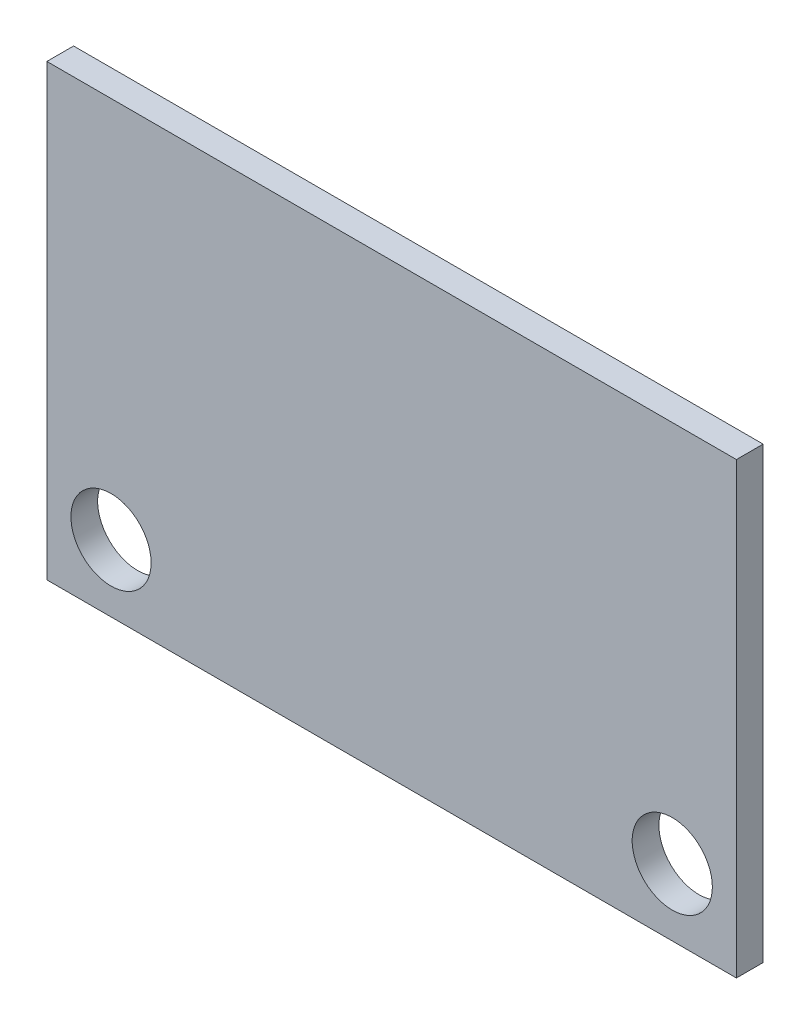
SolidWorks part; units mm, degrees
ref_plane "Alzado" through (0, 0, 0) normal (0, 0, 1) x (1, 0, 0)
ref_plane "Planta" through (0, 0, 0) normal (0, 1, 0) x (1, 0, 0)
ref_plane "Vista lateral" through (0, 0, 0) normal (1, 0, 0) x (0, 0, -1)
sketch "Croquis1" plane through (0, 0, 0) normal (0, 0, 1) x (1, 0, 0)
  line L0 (-10.5, -5.9) -> (10.5, -5.9) construction
  line L1 (12.9, -8.4) -> (-12.9, -8.4)
  line L2 (12.9, -8.4) -> (12.9, 8.4)
  line L3 (12.9, 8.4) -> (-12.9, 8.4)
  line L4 (-12.9, -8.4) -> (-12.9, 8.4)
  line L5 (12.9, -8.4) -> (-12.9, 8.4) construction
  line L6 (12.9, 8.4) -> (-12.9, -8.4) construction
  line L7 (0, 0) -> (0, -5.9) construction
  circle A0 centre (-10.5, -5.9) radius 1.5
  circle A1 centre (10.5, -5.9) radius 1.5
  point P1 (0, 0)
  dimension "D4" = 3
  dimension "D1" = 25.8
  dimension "D2" = 16.8
  dimension "D3" = 21
  dimension "D5" = 2.5
extrude "Saliente-Extruir1" add sketch "Croquis1" along normal blind 1
